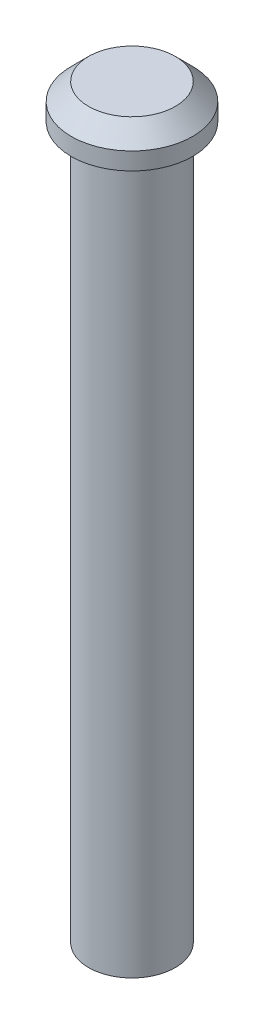
SolidWorks part; units mm, degrees
ref_plane "Front Plane" through (0, 0, 0) normal (0, 0, 1) x (1, 0, 0)
ref_plane "Top Plane" through (0, 0, 0) normal (0, 1, 0) x (1, 0, 0)
ref_plane "Right Plane" through (0, 0, 0) normal (1, 0, 0) x (0, 0, -1)
sketch "Sketch1" plane through (0, 0, 0) normal (0, 1, 0) x (1, 0, 0)
  circle A0 centre (0, 0) radius 2.5
  dimension "D1" = 5
extrude "Boss-Extrude1" add sketch "Sketch1" along normal blind 41
sketch "Sketch2" plane through (0, 41, 0) normal (0, 1, 0) x (1, 0, 0)
  circle A0 centre (0, 0) radius 3.5
  dimension "D1" = 7
extrude "Boss-Extrude2" add sketch "Sketch2" along normal blind 2
chamfer "Chamfer1" distance 1 angle 45 1 edges at (0, 43, 3.5)
sketch "Sketch3" plane through (0, 0, 0) normal (0, -1, 0) x (1, 0, 0)
  circle A0 centre (0, 0) radius 1.5
  dimension "D1" = 3
extrude "Cut-Extrude1" cut sketch "Sketch3" against normal blind 5
